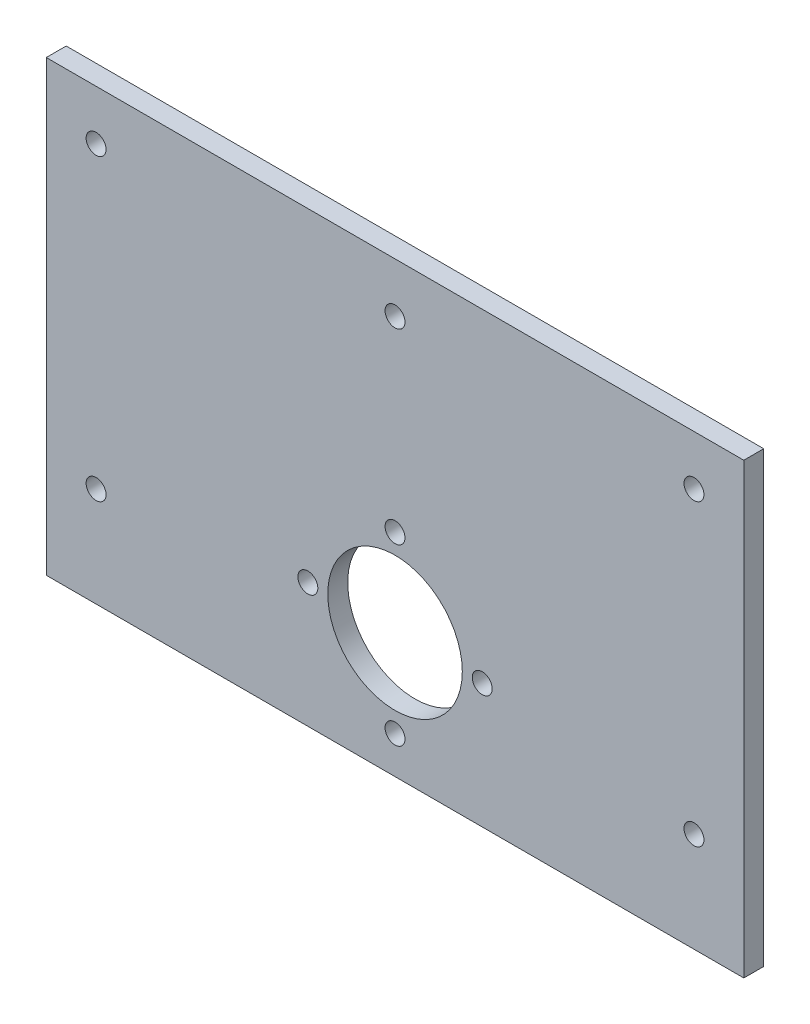
SolidWorks part; units mm, degrees
material "Epoxy, Unfilled"
ref_plane "Front Plane" through (0, 0, 0) normal (0, 0, 1) x (1, 0, 0)
ref_plane "Top Plane" through (0, 0, 0) normal (0, 1, 0) x (1, 0, 0)
ref_plane "Right Plane" through (0, 0, 0) normal (1, 0, 0) x (0, 0, -1)
sketch "Sketch1" plane through (0, 0, 0) normal (0, 0, 1) x (1, 0, 0)
  line L0 (0, 45) -> (0, -45) construction
  line L1 (-70, -45) -> (70, -45)
  line L2 (-70, -45) -> (-70, 45)
  line L3 (-70, 45) -> (70, 45)
  line L4 (70, -45) -> (70, 45)
  line L5 (-70, -45) -> (70, 45) construction
  line L6 (-70, 45) -> (70, -45) construction
  circle A1 centre (0, -20) radius 17.5 construction
  circle A2 centre (0, -2.5) radius 2
  circle A3 centre (17.5, -20) radius 2
  circle A4 centre (0, -37.5) radius 2
  circle A5 centre (-17.5, -20) radius 2
  circle A6 centre (0, -20) radius 13.5
  point P0 (0, 0)
  point P21 (0, -20)
  dimension "D3" = 35
  dimension "D4" = 4
  dimension "D7" = 27
  dimension "D1" = 90
  dimension "D2" = 140
  dimension "D6" = 25
  dimension "D5" = 4
extrude "Boss-Extrude1" add sketch "Sketch1" along normal blind 4
sketch "Sketch2" plane through (0, 0, 4) normal (0, 0, 1) x (1, 0, 0)
  line L0 (-70, 35) -> (70, 35) construction
  line L1 (-70, 45) -> (-70, -45) construction
  line L2 (70, -45) -> (70, 45) construction
  line L3 (-70, 0) -> (70, 0) construction
  line L4 (70, 45) -> (-70, 45) construction
  circle A0 centre (0, 35) radius 2
  circle A1 centre (-60, 35) radius 2
  circle A2 centre (60, 35) radius 2
  dimension "D1" = 60
  dimension "D2" = 60
  dimension "D3" = 4
  dimension "D4" = 4
  dimension "D5" = 4
  dimension "D6" = 10
extrude "Cut-Extrude1" cut sketch "Sketch2" against normal through all
sketch "Sketch3" plane through (0, 0, 4) normal (0, 0, 1) x (1, 0, 0)
  line L0 (-60, 35) -> (-60, -45) construction
  line L1 (0, 45) -> (0, 0) construction
  line L2 (70, 45) -> (-70, 45) construction
  line L3 (-70, -45) -> (70, -45) construction
  circle A0 centre (-60, -25) radius 2
  circle A1 centre (-60, -85) radius 2
  circle A2 centre (-60, 35) radius 2 construction
  circle A3 centre (60, -85) radius 2
  circle A4 centre (60, -25) radius 2
  dimension "D1" = 60
  dimension "D2" = 60
  dimension "D3" = 4
  dimension "D4" = 4
extrude "Cut-Extrude2" cut sketch "Sketch3" against normal through all
